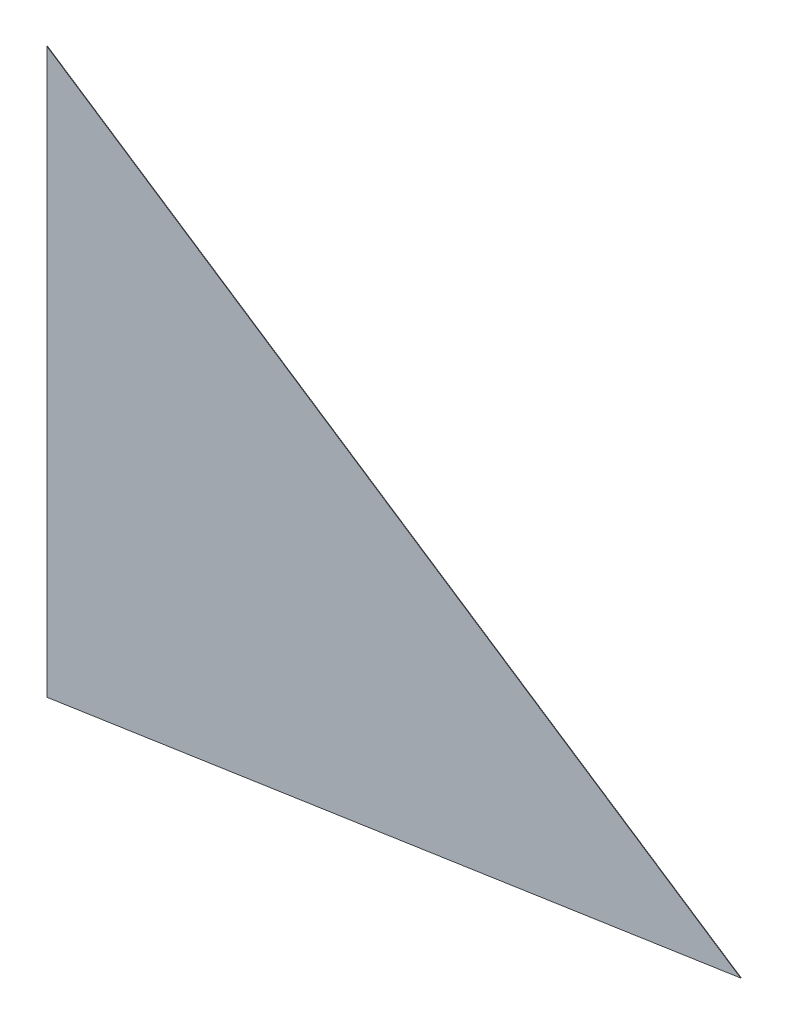
SolidWorks part; units mm, degrees
material "Hexcel AS4C (3000 Filamentów)"
ref_plane "Front Plane" through (0, 0, 0) normal (0, 0, 1) x (1, 0, 0)
ref_plane "Top Plane" through (0, 0, 0) normal (0, 1, 0) x (1, 0, 0)
ref_plane "Right Plane" through (0, 0, 0) normal (1, 0, 0) x (0, 0, -1)
sketch "Szkic1" plane through (0, 0, 0) normal (0, 0, 1) x (1, 0, 0)
  line L6 (-233.8753, -176.8408) -> (-903.9239, -277.0091)
  line L7 (-233.8753, -176.8408) -> (-903.9239, 267.5253)
  line L8 (-903.9239, 267.5253) -> (-903.9239, -277.0091)
extrude "Dodanie-wyciągnięcie1" add sketch "Szkic1" along normal blind 0.5 contours L8 L6 L7
